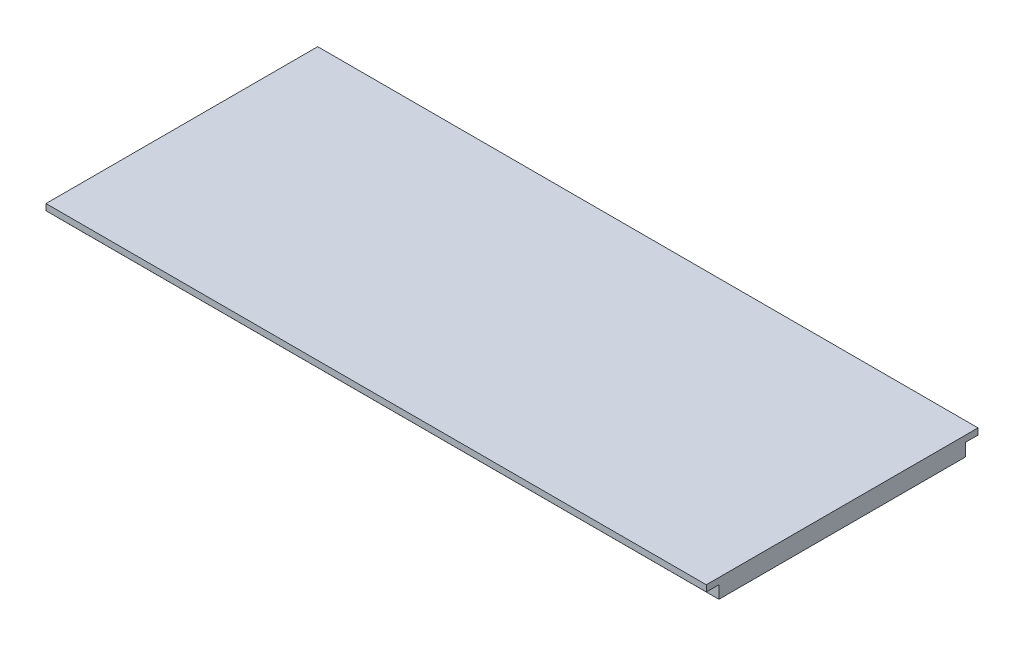
SolidWorks part; units mm, degrees
material "ABS"
ref_plane "Front Plane" through (0, 0, 0) normal (0, 0, 1) x (1, 0, 0)
ref_plane "Top Plane" through (0, 0, 0) normal (0, 1, 0) x (1, 0, 0)
ref_plane "Right Plane" through (0, 0, 0) normal (1, 0, 0) x (0, 0, -1)
ref_plane "Plane1" through (-151.5589, 0, 0) normal (-1, 0, 0) x (0, 0, 1)
sketch "Sketch1" plane through (-151.5589, 0, 0) normal (-1, 0, 0) x (0, 0, 1)
  line L0 (59.0854, -1.3949) -> (59.0854, 1.6051) construction
  line L1 (39.0854, -1.3949) -> (79.0854, -1.3949) construction
  line L2 (37.5854, 1.6051) -> (80.5854, 1.6051) construction
  line L6 (37.5854, 1.6051) -> (80.5854, 1.6051)
  line L7 (39.5854, -1.3949) -> (78.5854, -1.3949)
  line L8 (78.5854, -1.3949) -> (78.5854, 0.6131)
  line L12 (37.5854, 0.6131) -> (37.5854, 1.6051)
  line L13 (39.5854, 0.6131) -> (37.5854, 0.6131)
  line L14 (39.5854, -1.3949) -> (39.5854, 0.6131)
  line L15 (78.5854, 0.6131) -> (80.5854, 0.6131)
  line L16 (80.5854, 0.6131) -> (80.5854, 1.6051)
  line L17 (78.5854, -1.3949) -> (78.5854, 0.6131)
  line L18 (78.5854, 0.6131) -> (80.5854, 0.6131)
  line L19 (80.5854, 0.6131) -> (80.5854, 1.6051)
  dimension "D2" = 2
  dimension "D1" = 2.008
  dimension "D3" = 0.992
  dimension "D4" = 39
extrude "Boss-Extrude1" add sketch "Sketch1" against normal offset from surface (104.492 mm away) 0.508 contours L7 L0 L6 L12 L13 L14 | L0 L7 L8 L15 L16 L6
sketch "Sketch2" plane through (-151.5589, 0, 0) normal (-1, 0, 0) x (0, 0, 1)
  line L0 (39.5854, -1.3949) -> (78.5854, -1.3949) construction
  line L3 (59.5668, -1.3949) -> (62.9685, -1.3949)
  arc A0 (37.3846, -4.5486) -> (37.8824, -5.717) centre (37.5949, -5.1492) ccw
  spline S0 degree 3 poles (59.5668, -1.3949) (61.5161, -1.4803) (64.6149, -4.0489) (61.888, -9.9075) (51.2562, -7.0931) (44.0648, -1.7024) (37.3846, -4.5486) knots 0 0 0 0 0.142255 0.248972 0.491101 1 1 1 1
  spline S3 degree 1 poles (59.6224, -0.1261) (37.8824, -5.717) knots 0 0 1 1 construction
  spline S4 degree 3 poles (59.6224, -0.1261) (60.1681, -0.15) (61.2715, -0.3736) (62.6836, -1.1022) (63.8439, -2.1428) (64.6754, -3.4393) (65.0113, -5.0128) (64.7612, -6.4772) (64.1588, -7.7456) (63.2941, -8.7948) (62.2263, -9.5482) (60.66, -10.1159) (58.6401, -10.1492) (56.2634, -9.5893) (53.2148, -8.4481) (49.7568, -6.8066) (46.5227, -5.4549) (43.981, -4.8621) (42.0621, -4.7194) (40.3935, -4.909) (38.9981, -5.2811) (38.243, -5.5633) (37.8824, -5.717) knots 0 0 0 0 0.03125 0.0625 0.09375 0.125 0.15625 0.1875 0.21875 0.25 0.28125 0.3125 0.375 0.4375 0.5 0.625 0.75 0.8125 0.875 0.9375 0.96875 1 1 1 1 only from (62.9685, -1.3949) to (37.8824, -5.717)
  dimension "D2" = 1.27
extrude "Boss-Extrude2" add sketch "Sketch2" along normal blind 38.1 from offset 63.5 offset against normal yes
ref_plane "Plane2" through (0, -1.3949, 0) normal (0, -1, 0) x (-1, 0, 0)
sketch "Sketch3" plane through (0, -1.3949, 0) normal (0, -1, 0) x (-1, 0, 0)
  line L8 (118.5389, -57.2956) -> (118.5389, -45.5024)
  line L9 (118.5389, -45.5024) -> (95.6789, -45.5024)
  line L10 (95.6789, -45.5024) -> (95.6789, -57.2956)
  line L11 (95.6789, -57.2956) -> (118.5389, -57.2956)
  line L12 (118.5389, -57.2956) -> (118.5389, -45.5024)
  line L13 (118.5389, -45.5024) -> (95.6789, -45.5024)
  line L14 (95.6789, -45.5024) -> (95.6789, -57.2956)
  line L15 (95.6789, -57.2956) -> (118.5389, -57.2956)
  dimension "D1" = 7.62
extrude "Cut-Extrude1" cut sketch "Sketch3" along normal up to surface (3.8425 mm away)
